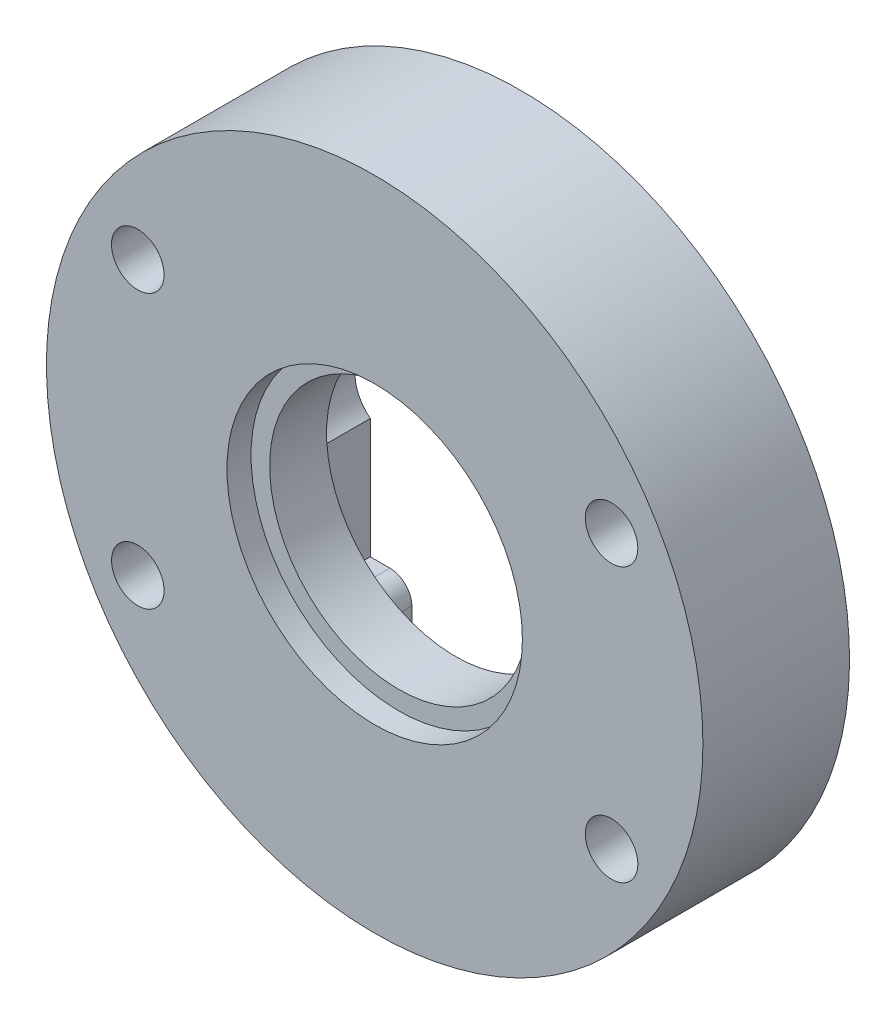
SolidWorks part; units mm, degrees
ref_plane "정면" through (0, 0, 0) normal (0, 0, 1) x (1, 0, 0)
ref_plane "윗면" through (0, 0, 0) normal (0, 1, 0) x (1, 0, 0)
ref_plane "우측면" through (0, 0, 0) normal (1, 0, 0) x (0, 0, -1)
sketch "스케치1" plane through (0, 0, 0) normal (0, 0, 1) x (1, 0, 0)
  line L0 (-5, -6.9) -> (-6.9, -6.9)
  line L2 (-5, -6.9) -> (-5, -14.1421)
  line L3 (0, -6.9) -> (0, -15) construction
  line L4 (5, -6.9) -> (5, -14.1421)
  line L6 (6.9, -6.9) -> (5, -6.9)
  line L7 (6.9, -6.9) -> (6.9, 6.9)
  line L8 (6.9, 6.9) -> (-6.9, 6.9)
  line L9 (-6.9, -6.9) -> (-6.9, 6.9)
  arc A0 (5, -14.1421) -> (-5, -14.1421) centre (0, 0) ccw
  circle A2 centre (0, 9.5) radius 2.1 construction
  circle A3 centre (0, 0) radius 9.5 construction
  point P1 (0, 6.9)
  point P10 (4.25, -14.25)
  point P15 (6.9, 0)
  point P16 (2.6661, -6.9)
  point P18 (0, -15.356)
  point P19 (0, 0)
  point P20 (0, 0)
  point P22 (0, 9.5)
  point P23 (4.25, -14.3853)
  point P28 (0, 0)
  dimension "D1" = 30
  dimension "D2" = 4.2
  dimension "D6" = 13.8
  dimension "D7" = 5
  dimension "D8" = 13.8
  dimension "D3" = 19
extrude "보스-돌출1" add sketch "스케치1" along normal blind 3
sketch "스케치11" plane through (0, 0, 3) normal (0, 0, 1) x (1, 0, 0)
  line L0 (5.8, 0) -> (-5.8, 0) construction
  line L1 (5.8, 0) -> (-5.8, 0) construction
  line L2 (5.8, -1.8) -> (-5.8, -1.8)
  line L3 (5.8, 1.8) -> (-5.8, 1.8)
  arc A0 (5.8, -1.8) -> (5.8, 1.8) centre (5.8, 0) ccw
  arc A1 (-5.8, 1.8) -> (-5.8, -1.8) centre (-5.8, 0) ccw
  point P4 (0, 0)
  point P6 (0, 0)
  dimension "D2" = 1.8
  dimension "D1" = 11.6
extrude "컷-돌출4" cut sketch "스케치11" against normal through all
sketch "스케치12" plane through (0, 0, 3) normal (0, 0, 1) x (1, 0, 0)
  circle A0 centre (0, 0) radius 15
  circle A1 centre (0, 0) radius 5.9
  dimension "D1" = 30
  dimension "D2" = 11.8
extrude "보스-돌출2" add sketch "스케치12" along normal blind 2.6
sketch "스케치13" plane through (0, 0, 5.6) normal (0, 0, 1) x (1, 0, 0)
  circle A0 centre (0, 0) radius 6.75
  circle A1 centre (0, 0) radius 15
  dimension "D1" = 13.5
  dimension "D2" = 30
extrude "보스-돌출3" add sketch "스케치13" along normal blind 1.1
sketch "스케치14" plane through (0, 0, 6.7) normal (0, 0, 1) x (1, 0, 0)
  line L0 (0, 0) -> (15, 0) construction
  line L1 (0, 0) -> (0, 15) construction
  line L2 (0, 0) -> (10.8253, 6.25) construction
  circle A0 centre (0, 0) radius 15 construction
  circle A1 centre (10.8253, 6.25) radius 1.2
  circle A2 centre (-10.8253, 6.25) radius 1.2
  circle A3 centre (10.8253, -6.25) radius 1.2
  circle A4 centre (-10.8253, -6.25) radius 1.2
  dimension "D1" = 2.4
  dimension "D2" = 12.5
  dimension "D3" = 60
extrude "컷-돌출5" cut sketch "스케치14" against normal through all
fillet "필렛1" radius 1 2 edges at (-5, -6.9, 1.5) (5, -6.9, 1.5)
